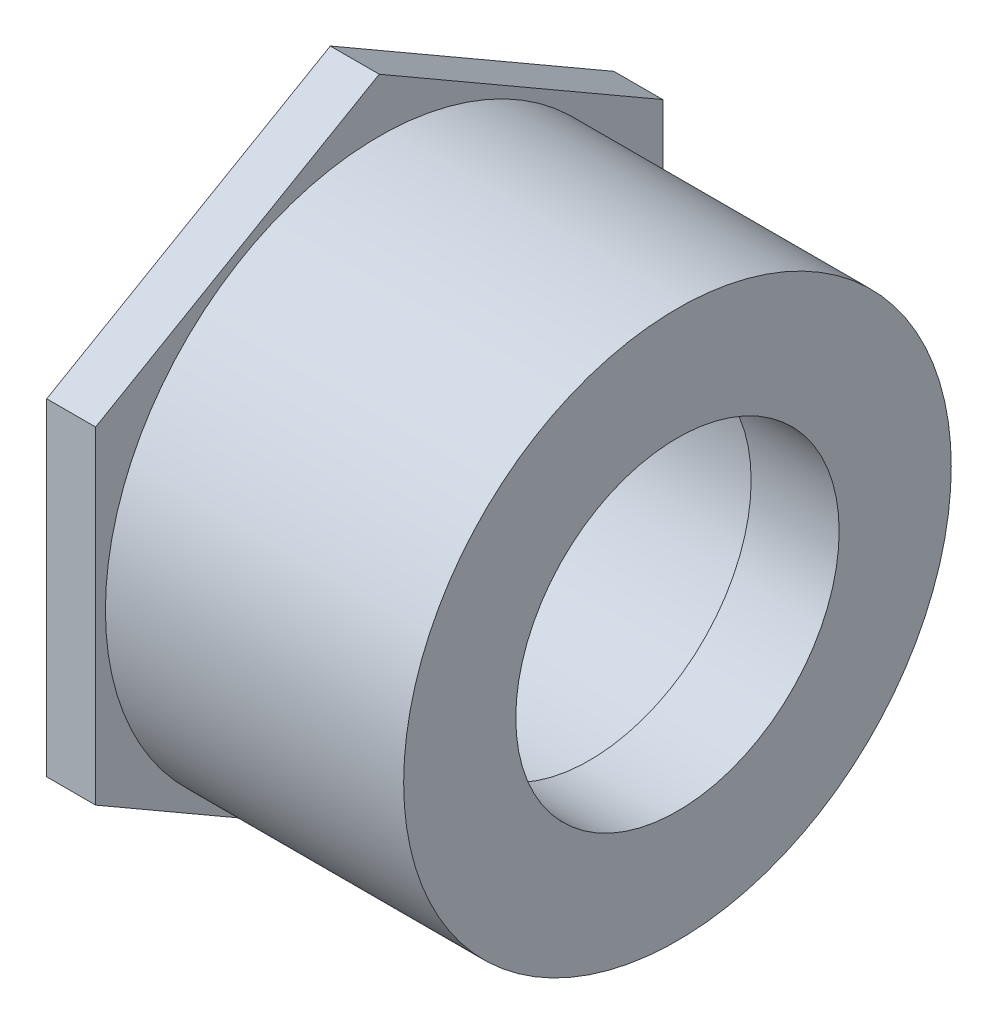
SolidWorks part; units mm, degrees
material "PVC Rigid"
ref_plane "Front Plane" through (0, 0, 0) normal (0, 0, 1) x (1, 0, 0)
ref_plane "Top Plane" through (0, 0, 0) normal (0, 1, 0) x (1, 0, 0)
ref_plane "Right Plane" through (0, 0, 0) normal (1, 0, 0) x (0, 0, -1)
sketch "Sketch0" plane through (0, 0, 0) normal (0, 0, 1) x (1, 0, 0)
  line L0 (-56.3562, 0) -> (0, 0) construction
  line L2 (-47.625, 44.45) -> (-47.625, -44.45) construction
  line L3 (-48.4187, 46.0375) -> (-48.4187, -46.0375) construction
  line L5 (-14.2875, 30.0863) -> (-56.3562, 30.3149) construction
  line L6 (-14.2875, 30.0863) -> (-14.2875, -30.0863) construction
  line L7 (-14.2875, -30.0863) -> (-56.3562, -30.3149) construction
  line L8 (-56.3562, 30.3149) -> (-56.3562, -30.3149) construction
  line L14 (-14.2875, 26.2509) -> (-14.2875, -26.2509) construction
  line L21 (-56.3562, 0) -> (-14.2875, 0) construction
  point P12 (-47.625, 0)
  point P27 (-48.4187, 0)
  dimension "A" = 56.3562
  dimension "OD A 2" = 60.6298
  dimension "OD B 2" = 60.1726
  dimension "ID 2" = 52.5018
  dimension "B" = 14.2875
  dimension "Pipe OD 1" = 88.9
  dimension "C 1" = 47.625
  dimension "J" = 92.075
  dimension "K" = 7.9375
sketch "Sketch1" plane through (0, 0, 0) normal (0, 0, 1) x (1, 0, 0)
  line L0 (-56.3562, 0) -> (0, 0) construction
  line L1 (-56.3562, 0) -> (0, 0) construction
  line L2 (-56.3562, -44.45) -> (0, -44.45)
  line L3 (0, -26.2509) -> (0, -44.45)
  line L4 (-56.3562, -44.45) -> (-56.3562, -30.3149)
  line L5 (-56.3562, -30.3149) -> (-14.2875, -30.0863)
  line L6 (0, 0) -> (0, -26.2509) construction
  line L8 (-14.2875, -26.2509) -> (-14.2875, -30.0863)
  line L11 (-14.2875, -26.2509) -> (0, -26.2509)
revolve "Revolve1" add sketch "Sketch1" angle 360 about L1
sketch "Sketch2" plane through (-56.3562, 0, 0) normal (-1, 0, 0) x (0, 0, 1)
  line L0 (0, 0) -> (0, 53.1595) construction
  line L1 (0, 53.1595) -> (-46.0375, 26.5798)
  line L2 (-46.0375, 26.5798) -> (-46.0375, -26.5798)
  line L3 (-46.0375, -26.5798) -> (0, -53.1595)
  line L4 (0, -53.1595) -> (46.0375, -26.5798)
  line L5 (46.0375, -26.5798) -> (46.0375, 26.5798)
  line L6 (46.0375, 26.5798) -> (0, 53.1595)
  circle A0 centre (0, 0) radius 30.3149 construction
  circle A1 centre (0, 0) radius 30.3149
  circle A2 centre (0, 0) radius 46.0375 construction
  point P3 (0, 46.0375)
extrude "Boss-Extrude1" add sketch "Sketch2" against normal up to vertex (7.9375 mm away) up to point (-48.4187, 0, 0)
